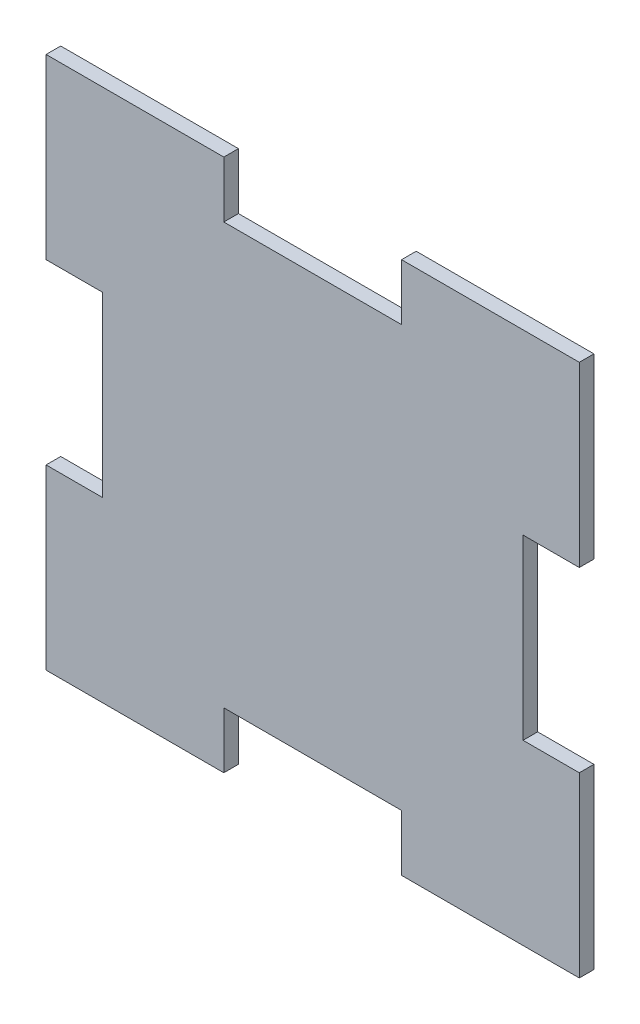
SolidWorks part; units mm, degrees
ref_plane "Front Plane" through (0, 0, 0) normal (0, 0, 1) x (1, 0, 0)
ref_plane "Top Plane" through (0, 0, 0) normal (0, 1, 0) x (1, 0, 0)
ref_plane "Right Plane" through (0, 0, 0) normal (1, 0, 0) x (0, 0, -1)
sketch "Sketch1" plane through (0, 0, 0) normal (0, 0, 1) x (1, 0, 0)
  line L2 (1.1204, 67.1976) -> (1.1204, 32.2376)
  line L5 (31.0404, 2.3176) -> (66.0004, 2.3176)
  line L6 (95.9204, 32.2376) -> (95.9204, 62.1576)
  line L8 (1.1204, 97.1176) -> (1.1204, 67.1976)
  line L9 (60.9604, 97.1176) -> (31.0404, 97.1176)
  line L12 (1.1204, 2.3176) -> (1.1204, 32.2376)
  line L15 (1.1204, 97.1176) -> (31.0404, 97.1176)
  line L19 (95.9204, 97.1176) -> (60.9604, 97.1176)
  line L22 (95.9204, 97.1176) -> (95.9204, 62.1576)
  line L27 (95.9204, 2.3176) -> (66.0004, 2.3176)
  line L28 (95.9204, 32.2376) -> (95.9204, 2.3176)
  line L33 (1.1204, 2.3176) -> (31.0404, 2.3176)
  dimension "D1" = 94.8
  dimension "D2" = 94.8
extrude "Boss-Extrude1" add sketch "Sketch1" along normal blind 2.6
sketch "Sketch2" plane through (0, 0, 2.6) normal (0, 0, 1) x (1, 0, 0)
  line L0 (1.1204, 49.7176) -> (50001.1204, 49.7176) construction
  line L1 (1.1204, 33.9176) -> (1.1204, 65.5176)
  line L2 (48.5204, 97.1176) -> (48.5204, 2.3176) construction
  line L3 (95.9204, 33.9176) -> (85.9204, 33.9176)
  line L4 (1.1204, 97.1176) -> (1.1204, 2.3176) construction
  line L5 (95.9204, 2.3176) -> (95.9204, 97.1176) construction
  line L6 (95.9204, 33.9176) -> (95.9204, 65.5176)
  line L7 (95.9204, 97.1176) -> (1.1204, 97.1176) construction
  line L8 (95.9204, 65.5176) -> (85.9204, 65.5176)
  line L9 (85.9204, 33.9176) -> (85.9204, 65.5176)
  line L10 (1.1204, 2.3176) -> (95.9204, 2.3176) construction
  line L11 (1.1204, 33.9176) -> (11.1204, 33.9176)
  line L12 (11.1204, 33.9176) -> (11.1204, 65.5176)
  line L13 (1.1204, 65.5176) -> (11.1204, 65.5176)
  line L14 (32.7204, 97.1176) -> (1.1204, 97.1176) construction
  line L15 (32.7204, 97.1176) -> (64.3204, 97.1176)
  line L16 (95.9204, 97.1176) -> (95.9204, 65.5176) construction
  line L17 (32.7204, 97.1176) -> (32.7204, 87.1176)
  line L18 (32.7204, 87.1176) -> (64.3204, 87.1176)
  line L19 (64.3204, 97.1176) -> (64.3204, 87.1176)
  line L20 (95.9204, 97.1176) -> (64.3204, 97.1176) construction
  line L21 (95.9204, 33.9176) -> (95.9204, 2.3176) construction
  line L22 (32.7204, 12.3176) -> (64.3204, 12.3176)
  line L23 (64.3204, 2.3176) -> (64.3204, 12.3176)
  line L24 (32.7204, 2.3176) -> (64.3204, 2.3176)
  line L25 (32.7204, 2.3176) -> (32.7204, 12.3176)
  point P10 (1.1204, 49.7176)
  point P13 (95.9204, 49.7176)
  point P26 (46.1848, 47.8176)
  dimension "D1" = 10
  dimension "D2" = 10
extrude "Cut-Extrude1" cut sketch "Sketch2" against normal through all
equation "\"mdf\"=\"mdf@fmv1.assembly\""
equation "\"D1@Boss-Extrude1\"=\"mdf\""
equation "\"D1@Sketch1\" = 100-2*\"mdf\""
equation "\"D2@Sketch1\" = 100-2*\"mdf\""
